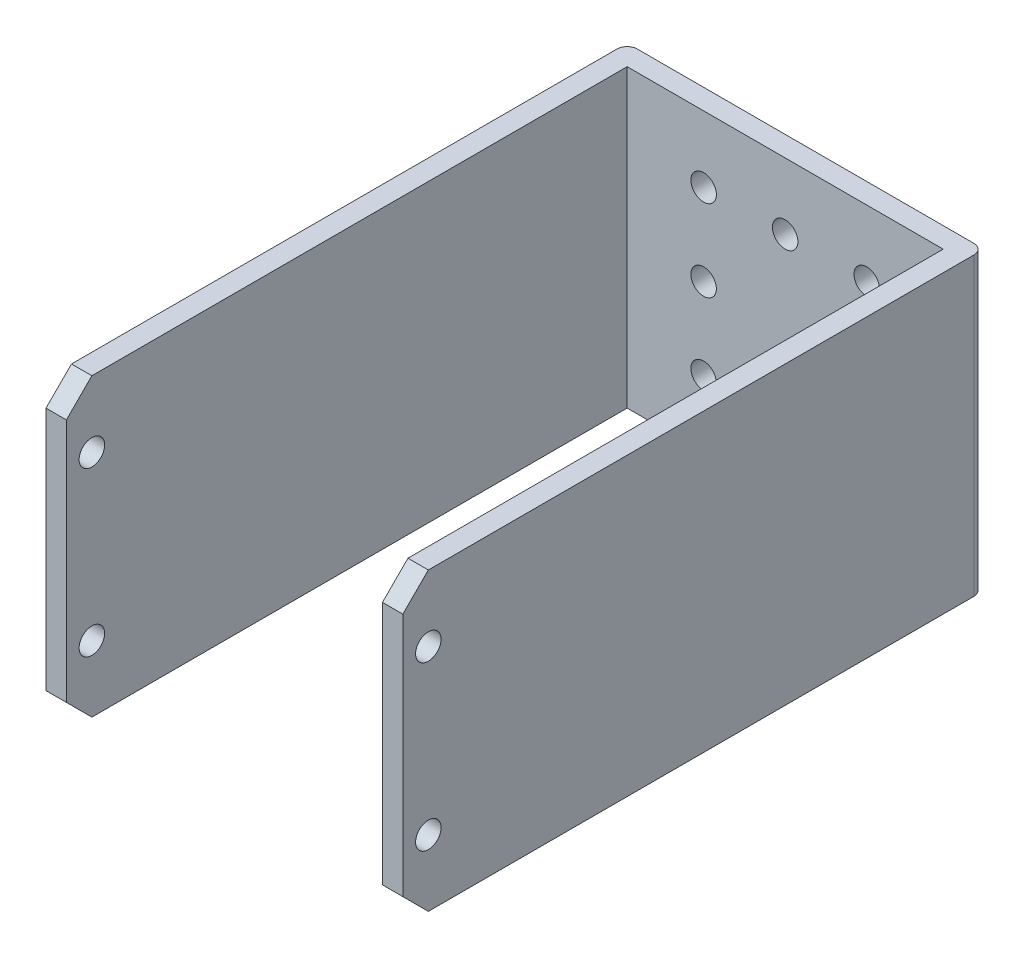
SolidWorks part; units mm, degrees
ref_plane "Front Plane" through (0, 0, 0) normal (0, 0, 1) x (1, 0, 0)
ref_plane "Top Plane" through (0, 0, 0) normal (0, 1, 0) x (1, 0, 0)
ref_plane "Right Plane" through (0, 0, 0) normal (1, 0, 0) x (0, 0, -1)
sketch "Sketch1" plane through (0, 0, 0) normal (0, 0, 1) x (1, 0, 0)
  line L1 (35, 0) -> (0, 0)
  line L2 (35, 0) -> (35, 29)
  line L3 (35, 29) -> (0, 29)
  line L4 (0, 0) -> (0, 29)
  point P6 (17.5, 0)
  dimension "D1" = 35
  dimension "D2" = 29
  dimension "D3" = 0
  dimension "D4" = 0
extrude "Boss-Extrude1" add sketch "Sketch1" along normal blind 57
sketch "Sketch3" plane through (0, 0, 57) normal (0, 0, 1) x (1, 0, 0)
  line L0 (35, 29) -> (0, 29) construction
  line L1 (2, 29) -> (33, 29)
  line L2 (2, 29) -> (2, 0)
  line L3 (2, 0) -> (33, 0)
  line L4 (33, 29) -> (33, 0)
  line L5 (0, 29) -> (0, 0) construction
  line L6 (35, 0) -> (35, 29) construction
  point P6 (2, 14.5)
  point P11 (33, 14.5)
  dimension "D1" = 2
  dimension "D2" = 29
  dimension "D3" = 2
extrude "Cut-Extrude1" cut sketch "Sketch3" against normal blind 55
fillet "Fillet1" radius 1 2 edges at (35, 14.5, 0) (0, 14.5, 0)
chamfer "Chamfer1" distance 2.5 4 edges at (34, 0, 57) (1, 0, 57) (34, 29, 57) (1, 29, 57)
sketch "Sketch4" plane through (0, 0, 0) normal (-1, 0, 0) x (0, 0, 1)
  line L0 (54.5, 29) -> (1, 29) construction
  line L1 (57, 26.5) -> (57, 2.5) construction
  circle A0 centre (54.5, 22.5) radius 1.25
  circle A1 centre (54.5, 6.5) radius 1.25
  dimension "D1" = 2.5
  dimension "D2" = 6.5
  dimension "D3" = 2.5
  dimension "D5" = 16
  dimension "D4" = 2
extrude "Cut-Extrude2" cut sketch "Sketch4" against normal blind 40.5
sketch "Sketch7" plane through (0, 0, 2) normal (0, 0, 1) x (1, 0, 0)
  line L1 (1, 0) -> (34, 0) construction
  line L3 (2, 29) -> (2, 0) construction
  circle A8 centre (9.5, 6.5) radius 1.25
  circle A9 centre (17.5, 6.5) radius 1.25
  circle A10 centre (25.5, 6.5) radius 1.25
  circle A11 centre (17.5, 14.5) radius 1.25 [skipped]
  circle A12 centre (25.5, 14.5) radius 1.25
  circle A13 centre (17.5, 22.5) radius 1.25
  circle A14 centre (25.5, 22.5) radius 1.25
  circle A15 centre (9.5, 14.5) radius 1.25
  circle A16 centre (9.5, 22.5) radius 1.25
  dimension "D2" = 2.5
  dimension "D7" = 8
  dimension "D4" = 3
  dimension "D5" = 3
  dimension "D3" = 7.5
  dimension "D6" = 8
  dimension "D17" = 6.5
extrude "Cut-Extrude3" cut sketch "Sketch7" against normal blind 5
